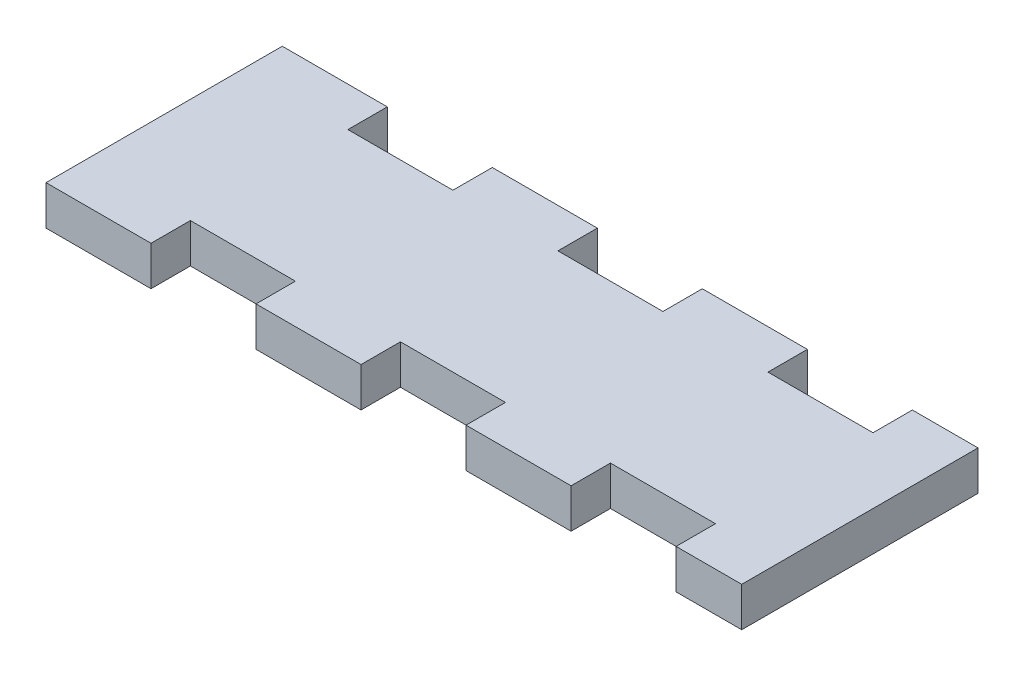
SolidWorks part; units mm, degrees
ref_plane "Front" through (0, 0, 0) normal (0, 0, 1) x (1, 0, 0)
ref_plane "Top" through (0, 0, 0) normal (0, 1, 0) x (1, 0, 0)
ref_plane "Right" through (0, 0, 0) normal (1, 0, 0) x (0, 0, -1)
sketch "Skizze1" plane through (0, 0, 0) normal (0, 1, 0) x (1, 0, 0)
  line L1 (0, 0) -> (53, 0) construction
  line L2 (0, 0) -> (0, 18) construction
  line L3 (0, 18) -> (53, 18) construction
  line L4 (53, 0) -> (53, 18) construction
  line L116 (0, 0) -> (7.9997, 0)
  line L117 (7.9997, 3) -> (7.9997, 0)
  line L118 (7.9997, 3) -> (15.9992, 3)
  line L119 (15.9992, 3) -> (15.9992, 0)
  line L120 (15.9992, 0) -> (24.0002, 0)
  line L121 (24.0002, 3) -> (24.0002, 0)
  line L122 (24.0002, 3) -> (31.9994, 3)
  line L123 (31.9994, 3) -> (31.9994, 0)
  line L124 (31.9994, 0) -> (39.9992, 0)
  line L125 (39.9992, 3) -> (39.9992, 0)
  line L126 (39.9992, 3) -> (48.0002, 3)
  line L127 (48.0002, 3) -> (48.0002, 0)
  line L128 (48.0002, 0) -> (52.9996, 0)
  line L129 (0, 17.9997) -> (7.9997, 17.9997)
  line L130 (7.9997, 17.9997) -> (7.9997, 14.9997)
  line L131 (7.9997, 14.9997) -> (15.9992, 14.9997)
  line L132 (15.9992, 17.9997) -> (15.9992, 14.9997)
  line L133 (15.9992, 17.9997) -> (24.0002, 17.9997)
  line L134 (24.0002, 17.9997) -> (24.0002, 14.9997)
  line L135 (24.0002, 14.9997) -> (31.9994, 14.9997)
  line L136 (31.9994, 17.9997) -> (31.9994, 14.9997)
  line L137 (31.9994, 17.9997) -> (39.9992, 17.9997)
  line L138 (39.9992, 17.9997) -> (39.9992, 14.9997)
  line L139 (39.9992, 14.9997) -> (48.0002, 14.9997)
  line L140 (48.0002, 17.9997) -> (48.0002, 14.9997)
  line L141 (48.0002, 17.9997) -> (52.9996, 17.9997)
  line L142 (0, 0) -> (0, 17.9997)
  line L143 (52.9996, 0) -> (52.9996, 17.9997)
  dimension "D1" = 18
  dimension "D2" = 53
extrude "Aufsatz-Linear austragen1" add sketch "Skizze1" along normal blind 3
